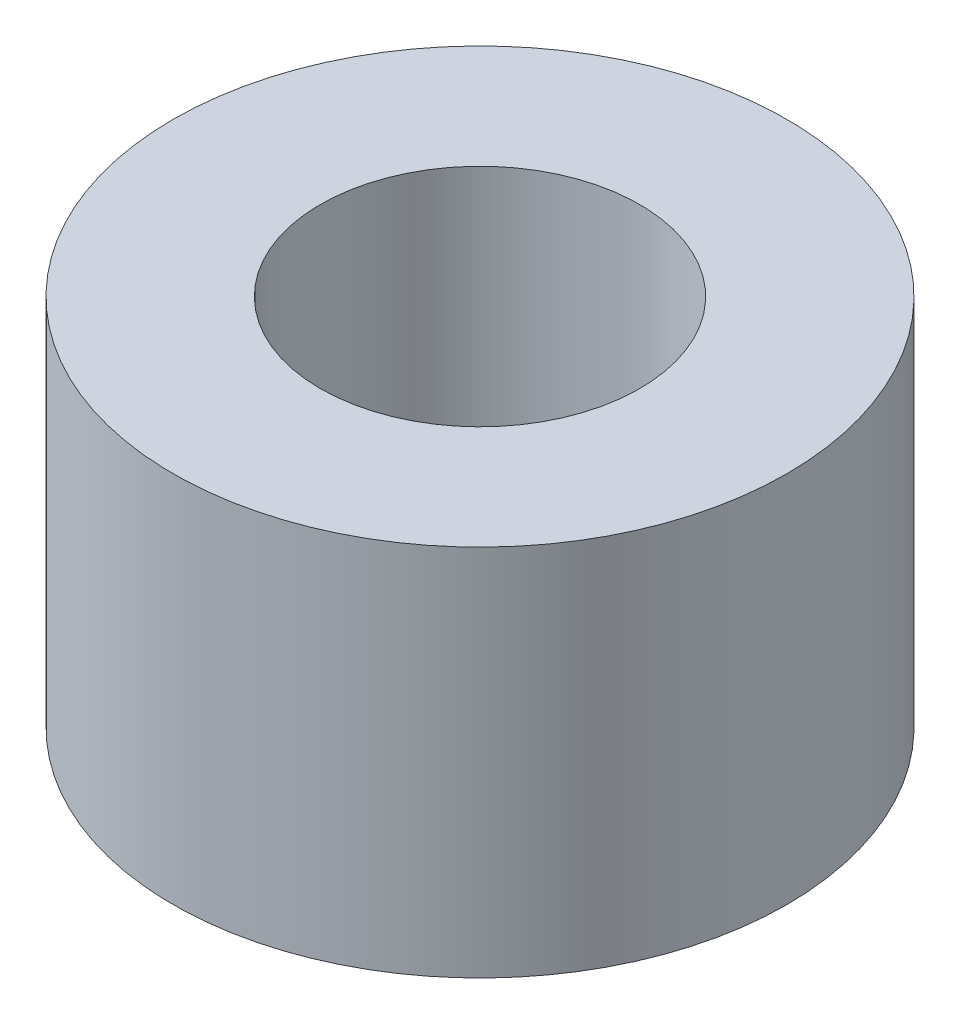
SolidWorks part; units mm, degrees
ref_plane "Front" through (0, 0, 0) normal (0, 0, 1) x (1, 0, 0)
ref_plane "Top" through (0, 0, 0) normal (0, 1, 0) x (1, 0, 0)
ref_plane "Right" through (0, 0, 0) normal (1, 0, 0) x (0, 0, -1)
sketch "Sketch1" plane through (0, 0, 0) normal (0, 1, 0) x (1, 0, 0)
  circle A0 centre (0, 0) radius 3.25
  dimension "D1" = 6.5
extrude "Extrude-Thin1" add sketch "Sketch1" along normal blind 7.6 thin
